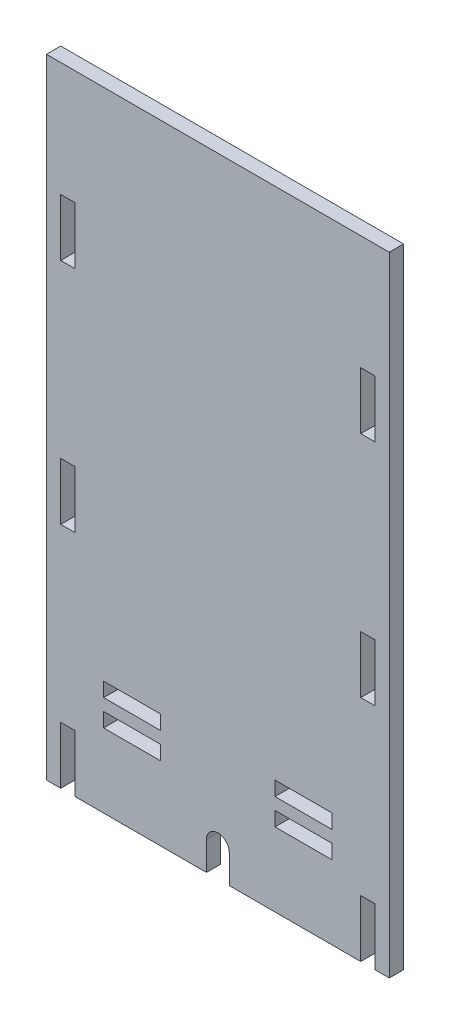
SolidWorks part; units mm, degrees
ref_plane "Front Plane" through (0, 0, 0) normal (0, 0, 1) x (1, 0, 0)
ref_plane "Top Plane" through (0, 0, 0) normal (0, 1, 0) x (1, 0, 0)
ref_plane "Right Plane" through (0, 0, 0) normal (1, 0, 0) x (0, 0, -1)
sketch "Sketch1" plane through (0, 0, 0) normal (0, 0, 1) x (1, 0, 0)
  line L1 (0, 0) -> (76.2, 0)
  line L2 (0, 0) -> (0, 139.7)
  line L3 (0, 139.7) -> (76.2, 139.7)
  line L4 (76.2, 0) -> (76.2, 139.7)
  dimension "D1" = 76.2
  dimension "D2" = 139.7
extrude "Extrude1" add sketch "Sketch1" along normal blind 3.175
sketch "Sketch2" plane through (0, 0, 3.175) normal (0, 0, 1) x (1, 0, 0)
  line L0 (38.1, 6.35) -> (38.1, -24.1777) construction
  line L1 (40.64, 6.35) -> (40.64, -24.1777)
  line L2 (35.56, 6.35) -> (35.56, -24.1777)
  line L3 (0, 0) -> (76.2, 0) construction
  line L4 (76.2, 0) -> (76.2, 139.7) construction
  arc A0 (40.64, 6.35) -> (35.56, 6.35) centre (38.1, 6.35) ccw
  arc A1 (35.56, -24.1777) -> (40.64, -24.1777) centre (38.1, -24.1777) ccw
  point P2 (38.1, -8.9138)
  dimension "D1" = 6.35
  dimension "D2" = 38.1
  dimension "D3" = 5.08
extrude "Extrude2" cut sketch "Sketch2" against normal through all
sketch "Sketch3" plane through (0, 0, 3.175) normal (0, 0, 1) x (1, 0, 0)
  line L0 (0, 139.7) -> (0, 0) construction
  line L1 (12.7, 25.4) -> (25.4, 25.4)
  line L2 (12.7, 25.4) -> (12.7, 22.225)
  line L3 (12.7, 22.225) -> (25.4, 22.225)
  line L4 (25.4, 25.4) -> (25.4, 22.225)
  line L6 (76.2, 139.7) -> (0, 139.7) construction
  dimension "D1" = 3.175
  dimension "D2" = 12.7
  dimension "D3" = 12.7
  dimension "D4" = 114.3
extrude "Extrude3" cut sketch "Sketch3" against normal through all
pattern_linear "LPattern1" count 2 spacing 38.1 along (1, 0, 0) count 2 spacing 5.842 along (0, -1, 0) of "Extrude3"
sketch "Sketch4" plane through (0, 0, 3.175) normal (0, 0, 1) x (1, 0, 0)
  line L0 (40.64, 0) -> (76.2, 0) construction
  line L1 (73.025, 0) -> (69.85, 0)
  line L2 (73.025, 0) -> (73.025, 12.7)
  line L3 (73.025, 12.7) -> (69.85, 12.7)
  line L4 (69.85, 0) -> (69.85, 12.7)
  line L5 (76.2, 0) -> (76.2, 139.7) construction
  dimension "D1" = 12.7
  dimension "D2" = 3.175
  dimension "D3" = 3.175
extrude "Extrude4" cut sketch "Sketch4" against normal through all
pattern_linear "LPattern2" count 3 spacing 50.8 along (0, 1, 0) count 2 spacing 66.675 along (-1, 0, 0) of "Extrude4"
